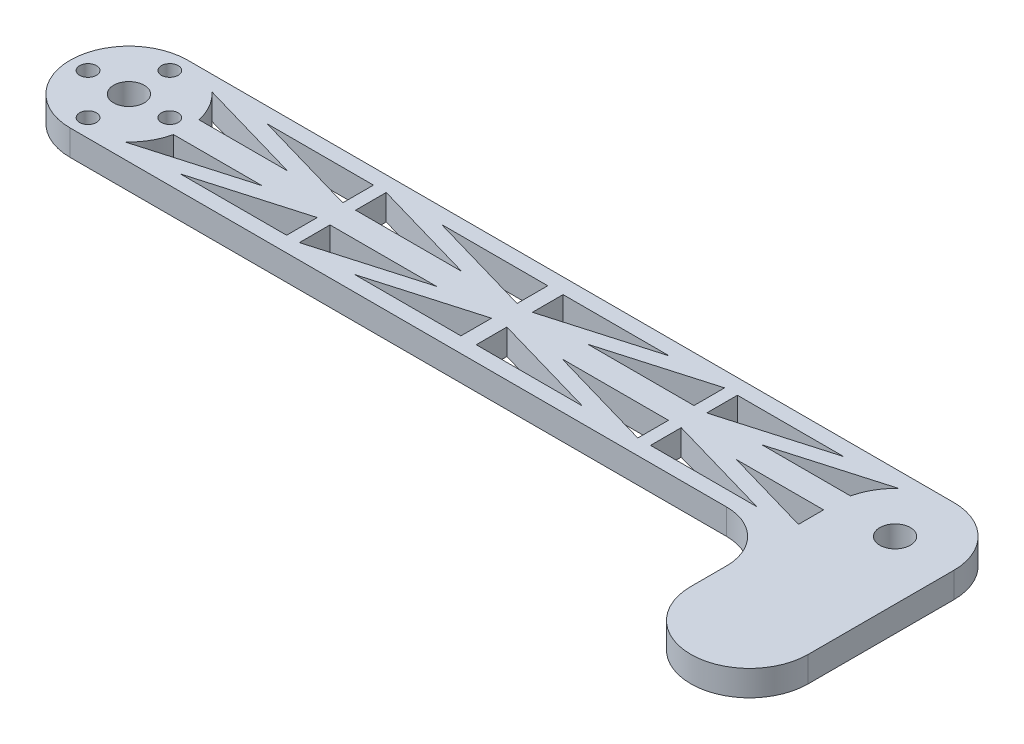
SolidWorks part; units mm, degrees
ref_plane "Front Plane" through (0, 0, 0) normal (0, 0, 1) x (1, 0, 0)
ref_plane "Top Plane" through (0, 0, 0) normal (0, 1, 0) x (1, 0, 0)
ref_plane "Right Plane" through (0, 0, 0) normal (1, 0, 0) x (0, 0, -1)
sketch "Sketch1" plane through (0, 0, 0) normal (0, 1, 0) x (1, 0, 0)
  line L0 (-75, 0) -> (75, 0) construction
  line L1 (-75, 11.5) -> (75, 11.5)
  line L2 (-75, -11.5) -> (75, -11.5)
  arc A0 (-75, 11.5) -> (-75, -11.5) centre (-75, 0) ccw
  arc A1 (75, -11.5) -> (75, 11.5) centre (75, 0) ccw
  circle A2 centre (-75, 8) radius 1.65
  circle A3 centre (-67, 0) radius 1.65
  circle A4 centre (-75, -8) radius 1.65
  circle A5 centre (-83, 0) radius 1.65
  circle A6 centre (75, 0) radius 3
  circle A7 centre (-75, 0) radius 3
  point P2 (0, 0)
  point P11 (-75, 0)
  point P20 (-75, 0)
  dimension "D1" = 11.5
  dimension "D3" = 3.3
  dimension "D6" = 6
  dimension "D7" = 6
  dimension "D2" = 150
  dimension "D4" = 8
  dimension "D5" = 4
extrude "Boss-Extrude1" add sketch "Sketch1" along normal blind 5
sketch "Sketch2" plane through (0, 5, 0) normal (0, 1, 0) x (1, 0, 0)
  line L0 (-75, 0) -> (75, 0) construction
  line L2 (-63.775, 2.5) -> (-46.452, 2.5)
  line L3 (-46.452, 2.5) -> (-67.254, 8.5)
  line L4 (-56.429, 8.5) -> (-35.627, 2.5)
  line L5 (-35.627, 2.5) -> (-35.627, 8.5)
  line L6 (-35.627, 8.5) -> (-56.429, 8.5)
  line L7 (75, 11.5) -> (-75, 11.5) construction
  line L8 (-12.325, 2.5) -> (-33.127, 8.5)
  line L9 (-33.127, 8.5) -> (-33.127, 2.5)
  line L10 (-33.127, 2.5) -> (-12.325, 2.5)
  line L11 (-1.5, 8.5) -> (-22.302, 8.5)
  line L12 (-22.302, 8.5) -> (-1.5, 2.5)
  line L13 (-1.5, 2.5) -> (-1.5, 8.5)
  line L14 (-46.452, 2.5) -> (-12.325, 2.5) construction
  line L15 (-1.5, -2.5) -> (-1.5, -8.5)
  line L16 (-22.302, -8.5) -> (-1.5, -2.5)
  line L17 (-1.5, -8.5) -> (-22.302, -8.5)
  line L18 (-33.127, -2.5) -> (-12.325, -2.5)
  line L19 (-33.127, -8.5) -> (-33.127, -2.5)
  line L20 (-12.325, -2.5) -> (-33.127, -8.5)
  line L21 (-35.627, -2.5) -> (-35.627, -8.5)
  line L22 (-56.429, -8.5) -> (-35.627, -2.5)
  line L23 (-35.627, -8.5) -> (-56.429, -8.5)
  line L24 (-46.452, -2.5) -> (-67.254, -8.5)
  line L25 (-63.775, -2.5) -> (-46.452, -2.5)
  line L26 (0, 0) -> (0, 11.5) construction
  line L27 (22.302, -8.5) -> (1.5, -2.5)
  line L28 (1.5, -8.5) -> (22.302, -8.5)
  line L29 (1.5, -2.5) -> (1.5, -8.5)
  line L30 (33.127, -8.5) -> (33.127, -2.5)
  line L31 (12.325, -2.5) -> (33.127, -8.5)
  line L32 (33.127, -2.5) -> (12.325, -2.5)
  line L33 (56.429, -8.5) -> (35.627, -2.5)
  line L34 (35.627, -8.5) -> (56.429, -8.5)
  line L35 (35.627, -2.5) -> (35.627, -8.5)
  line L36 (46.452, -2.5) -> (67.254, -8.5)
  line L37 (63.775, -2.5) -> (46.452, -2.5)
  line L38 (46.452, 2.5) -> (67.254, 8.5)
  line L39 (63.775, 2.5) -> (46.452, 2.5)
  line L40 (35.627, 2.5) -> (35.627, 8.5)
  line L41 (56.429, 8.5) -> (35.627, 2.5)
  line L42 (35.627, 8.5) -> (56.429, 8.5)
  line L43 (33.127, 2.5) -> (12.325, 2.5)
  line L44 (33.127, 8.5) -> (33.127, 2.5)
  line L45 (12.325, 2.5) -> (33.127, 8.5)
  line L46 (1.5, 2.5) -> (1.5, 8.5)
  line L47 (22.302, 8.5) -> (1.5, 2.5)
  line L48 (1.5, 8.5) -> (22.302, 8.5)
  circle A0 centre (-75, 0) radius 11.5 construction
  arc A1 (-67.254, 8.5) -> (-63.775, 2.5) centre (-75, 0) cw
  arc A2 (-67.254, -8.5) -> (-63.775, -2.5) centre (-75, 0) ccw
  arc A3 (67.254, -8.5) -> (63.775, -2.5) centre (75, 0) cw
  arc A4 (67.254, 8.5) -> (63.775, 2.5) centre (75, 0) ccw
  point P61 (-67.6117, 9)
  dimension "D1" = 1.5
  dimension "D2" = 3
  dimension "D3" = 3
  dimension "D4" = 2.5
  dimension "D6" = 2.5
  dimension "D5" = 2
extrude "Cut-Extrude1" cut sketch "Sketch2" against normal blind 5
sketch "Sketch3" plane through (0, 5, 0) normal (0, 1, 0) x (1, 0, 0)
  line L0 (75, 0) -> (75, -28.5) construction
  line L1 (86.5, 0) -> (86.5, -28.5)
  line L2 (63.5, 0) -> (63.5, -28.5)
  arc A0 (86.5, 0) -> (63.5, 0) centre (75, 0) ccw
  arc A1 (63.5, -28.5) -> (86.5, -28.5) centre (75, -28.5) ccw
  circle A2 centre (75, 0) radius 3 construction
  circle A3 centre (75, 0) radius 3
  arc A4 (75, -11.5) -> (75, 11.5) centre (75, 0) ccw construction
  point P3 (75, -14.25)
  point P15 (75, -40)
  dimension "D1" = 40
extrude "Boss-Extrude2" add sketch "Sketch3" against normal through all
fillet "Fillet1" radius 10 1 edges at (63.5, 2.5, 11.5)
